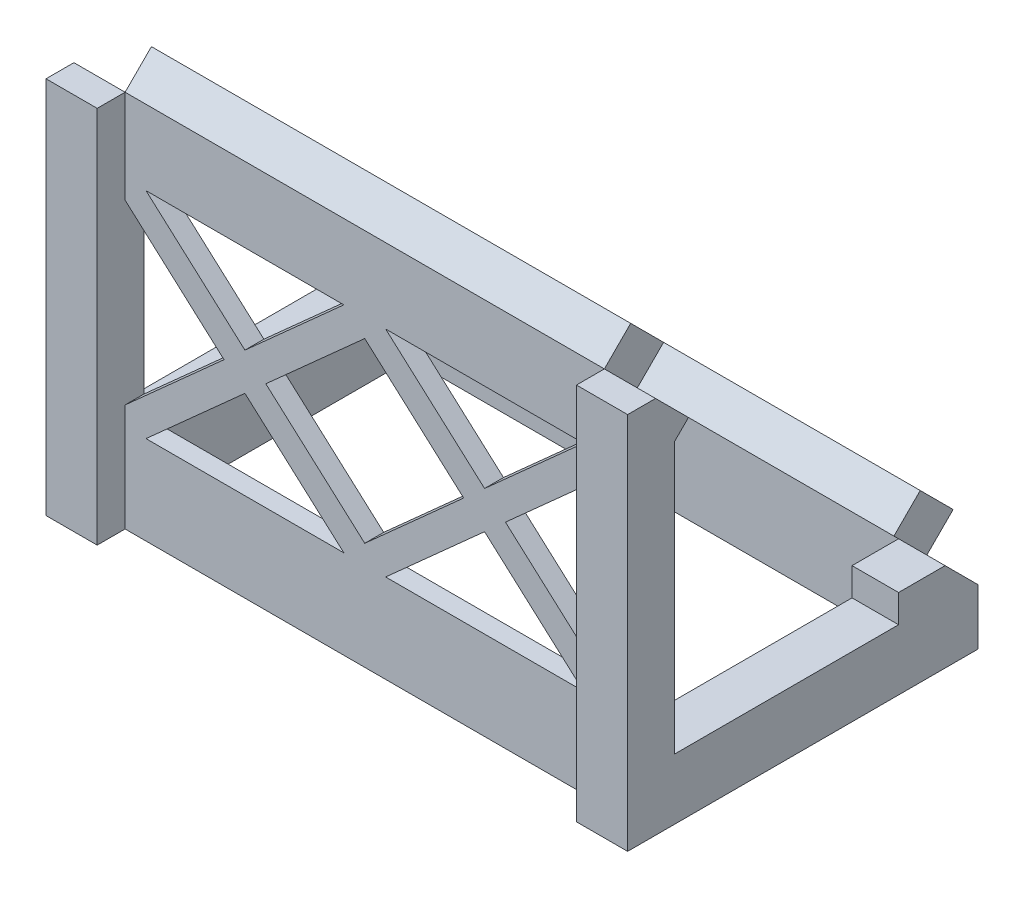
SolidWorks part; units mm, degrees
other "Markup1"
sketch "Sketch33" plane through (0, 74.9533, -74.9533) normal (0.1304, 0.6391, -0.758) x (-0.8301, -0.3477, -0.436)
ref_plane "Front Plane" through (0, 0, 0) normal (0, 0, 1) x (1, 0, 0)
ref_plane "Top Plane" through (0, 0, 0) normal (0, 1, 0) x (1, 0, 0)
ref_plane "Right Plane" through (0, 0, 0) normal (1, 0, 0) x (0, 0, -1)
sketch "Sketch1" plane through (0, 0, 0) normal (1, 0, 0) x (0, 0, -1)
  line L0 (0, 0) -> (69.2965, 0)
  line L1 (69.2965, 0) -> (0, 69.2965)
  line L2 (0, 69.2965) -> (0, 0)
  dimension "D1" = 45
  dimension "D2" = 98
extrude "Boss-Extrude3" add sketch "Sketch1" against normal blind 125
sketch "Sketch3" plane through (0, 0, 0) normal (0, -1, 0) x (1, 0, 0)
  line L1 (0, -69.2965) -> (-125, -69.2965)
  line L2 (0, -69.2965) -> (0, 0)
  line L3 (0, 0) -> (-125, 0)
  line L4 (-125, -69.2965) -> (-125, 0)
  line L5 (0, -69.2965) -> (-125, 0) construction
  line L6 (0, 0) -> (-125, -69.2965) construction
  point P4 (-62.5, -34.6482)
extrude "Boss-Extrude5" add sketch "Sketch3" along normal blind 12
sketch "Sketch6" plane through (-125, 0, 0) normal (-1, 0, 0) x (0, 0, 1)
  line L0 (-69.2965, 0) -> (-62.2254, 7.0711)
  line L1 (-69.2965, 0) -> (0, 69.2965) construction
  line L2 (0, 69.2965) -> (-7.0711, 62.2254)
  line L3 (-62.2254, 7.0711) -> (-7.0711, 7.0711)
  line L4 (-7.0711, 7.0711) -> (-7.0711, 62.2254)
  line L5 (-62.2254, 7.0711) -> (-7.0711, 62.2254)
  line M2 (0, 69.2965) -> (-69.2965, 0)
  dimension "D1" = 10
  dimension "D2" = 10
extrude "Cut-Extrude1" cut sketch "Sketch6" against normal through all contours L3 L4 M2
sketch "Sketch7" plane through (0, 34.6482, -34.6482) normal (0, 0.7071, -0.7071) x (1, 0, 0)
  line L0 (0, 39) -> (-10, 39)
  line L1 (0, 39) -> (-125, 39) construction
  line L2 (-125, 39) -> (-115, 39)
  line L3 (-125, 49) -> (0, 49) construction
  line L4 (-10, 39) -> (-115, 39)
  line L5 (-10, 39) -> (-10, 49)
  line L6 (-10, 49) -> (-115, 49)
  line L7 (-115, 39) -> (-115, 49)
  line L8 (-10, 39) -> (-115, 49) construction
  line L9 (-10, 49) -> (-115, 39) construction
  point P10 (-62.5, 44)
  line M3 (-125, 39) -> (0, 39)
  line M5 (0, 49) -> (-125, 49)
  dimension "D1" = 10
  dimension "D2" = 10
extrude "Boss-Extrude6" add sketch "Sketch7" along normal blind 8 contours L7 L5 M3 M5
sketch "Sketch8" plane through (0, 34.6482, -34.6482) normal (0, 0.7071, -0.7071) x (1, 0, 0)
  line L0 (0, -49) -> (-10, -49)
  line L1 (-125, -49) -> (0, -49) construction
  line L2 (-125, -49) -> (-115, -49)
  line L3 (0, -39) -> (-125, -39) construction
  line L4 (-10, -49) -> (-115, -49)
  line L5 (-10, -49) -> (-10, -39)
  line L6 (-10, -39) -> (-115, -39)
  line L7 (-115, -49) -> (-115, -39)
  line L8 (-10, -49) -> (-115, -39) construction
  line L9 (-10, -39) -> (-115, -49) construction
  point P10 (-62.5, -44)
  line M3 (0, -39) -> (-125, -39)
  line M5 (-125, -49) -> (0, -49)
  dimension "D1" = 10
  dimension "D2" = 10
extrude "Boss-Extrude7" add sketch "Sketch8" along normal blind 8 contours L7 L5 M5 M3
sketch "Sketch9" plane through (0, 7.0711, 0) normal (0, 1, 0) x (1, 0, 0)
  line L0 (0, 62.2254) -> (-10, 62.2254)
  line L1 (-125, 62.2254) -> (-115, 62.2254)
  line L2 (0, 7.0711) -> (-125, 7.0711) construction
  line L3 (-10, 62.2254) -> (-115, 62.2254)
  line L4 (-10, 62.2254) -> (-10, 7.0711)
  line L5 (-10, 7.0711) -> (-115, 7.0711)
  line L6 (-115, 62.2254) -> (-115, 7.0711)
  line L7 (-10, 62.2254) -> (-115, 7.0711) construction
  line L8 (-10, 7.0711) -> (-115, 62.2254) construction
  point P10 (-62.5, 34.6482)
  line M2 (-125, 7.0711) -> (0, 7.0711)
  line M5 (-10, 62.2254) -> (-115, 62.2254)
extrude "Cut-Extrude2" cut sketch "Sketch9" against normal through all contours L6 L4 M5 M2
sketch "Sketch11" plane through (0, 7.0711, 0) normal (0, 1, 0) x (1, 0, 0)
  line L1 (0, 62.2254) -> (-10, 62.2254)
  line L2 (0, 62.2254) -> (0, 7.0711)
  line L3 (0, 7.0711) -> (-10, 7.0711)
  line L4 (-10, 62.2254) -> (-10, 7.0711)
  line L5 (0, 62.2254) -> (-10, 7.0711) construction
  line L6 (0, 7.0711) -> (-10, 62.2254) construction
  point P4 (-5, 34.6482)
extrude "Cut-Extrude3" cut sketch "Sketch11" against normal blind 6
sketch "Sketch12" plane through (0, 7.0711, 0) normal (0, 1, 0) x (1, 0, 0)
  line L1 (-115, 62.2254) -> (-125, 62.2254)
  line L2 (-115, 62.2254) -> (-115, 7.0711)
  line L3 (-115, 7.0711) -> (-125, 7.0711)
  line L4 (-125, 62.2254) -> (-125, 7.0711)
  line L5 (-115, 62.2254) -> (-125, 7.0711) construction
  line L6 (-115, 7.0711) -> (-125, 62.2254) construction
  point P4 (-120, 34.6482)
extrude "Cut-Extrude4" cut sketch "Sketch12" against normal blind 6
sketch "Sketch13" plane through (0, 0, -7.0711) normal (0, 0, -1) x (-1, 0, 0)
  line L1 (10, 1.0711) -> (115, 1.0711)
  line L2 (10, 1.0711) -> (10, 62.2254)
  line L3 (10, 62.2254) -> (115, 62.2254)
  line L4 (115, 1.0711) -> (115, 62.2254)
  line L5 (10, 1.0711) -> (115, 62.2254) construction
  line L6 (10, 62.2254) -> (115, 1.0711) construction
  point P4 (62.5, 31.6482)
extrude "Cut-Extrude6" cut sketch "Sketch13" against normal blind 3
sketch "Sketch14" plane through (0, 34.6482, -34.6482) normal (0, 0.7071, -0.7071) x (1, 0, 0)
  line L0 (0, 49) -> (-6.25, 49)
  line L1 (-10, 49) -> (0, 49) construction
  line L2 (-6.25, 49) -> (-6.25, 42.75)
  circle A0 centre (-6.25, 42.75) radius 1.9
  dimension "D1" = 6.25
  dimension "D2" = 6.25
extrude "Cut-Extrude8" cut sketch "Sketch14" against normal blind 6
ref_plane "Plane1" through (-62.5, 0, 0) normal (1, 0, 0) x (0, 0, -1)
mirror "Mirror1" about plane through (-62.5, 0, 0) normal (1, 0, 0) of "Cut-Extrude8"
sketch "Sketch15" plane through (0, 34.6482, -34.6482) normal (0, 0.7071, -0.7071) x (1, 0, 0)
  line L0 (0, -49) -> (-6.25, -49)
  line L1 (-10, -49) -> (0, -49) construction
  line L2 (-6.25, -49) -> (-6.25, -42.75)
  circle A0 centre (-6.25, -42.75) radius 1.9
  dimension "D3" = 3.8
  dimension "D1" = 6.25
  dimension "D2" = 6.25
extrude "Cut-Extrude9" cut sketch "Sketch15" against normal blind 6
mirror "Mirror2" about plane through (-62.5, 0, 0) normal (1, 0, 0) of "Cut-Extrude9"
sketch "Sketch22" plane through (-10, 0, 0) normal (-1, 0, 0) x (0, 0, 1)
  line L0 (-7.0711, 62.2254) -> (-4.0711, 59.2254)
  line L1 (-4.0711, 62.2254) -> (-4.0711, 1.0711) construction
  line L2 (-4.0711, 59.2254) -> (-4.0711, 62.2254)
  line L3 (-4.0711, 62.2254) -> (-7.0711, 62.2254)
  line L4 (-12.7279, 67.8823) -> (-7.0711, 62.2254) construction
extrude "Boss-Extrude9" add sketch "Sketch22" along normal up to next
sketch "Sketch25" plane through (0, 0, -62.2254) normal (0, 0, 1) x (1, 0, 0)
  line L1 (-10, 1.0711) -> (0, 1.0711)
  line L2 (-10, 1.0711) -> (-10, 7.0711)
  line L3 (-10, 7.0711) -> (0, 7.0711)
  line L4 (0, 1.0711) -> (0, 7.0711)
  line L5 (-10, 1.0711) -> (0, 7.0711) construction
  line L6 (-10, 7.0711) -> (0, 1.0711) construction
  line L7 (-125, 1.0711) -> (-115, 1.0711)
  line L8 (-125, 1.0711) -> (-125, 7.0711)
  line L9 (-125, 7.0711) -> (-115, 7.0711)
  line L10 (-115, 1.0711) -> (-115, 7.0711)
  line L11 (-125, 1.0711) -> (-115, 7.0711) construction
  line L12 (-125, 7.0711) -> (-115, 1.0711) construction
  point P4 (-5, 4.0711)
  point P11 (-120, 4.0711)
extrude "Boss-Extrude13" add sketch "Sketch25" along normal blind 10
sketch "Sketch26" plane through (-10, 0, 0) normal (1, 0, 0) x (0, 0, -1)
  line L0 (0, 69.2965) -> (7.0711, 62.2254)
  line L1 (7.0711, 62.2254) -> (12.7279, 67.8823)
  line L2 (12.7279, 67.8823) -> (5.6569, 74.9533)
  line L3 (5.6569, 74.9533) -> (0, 69.2965)
extrude "Cut-Extrude10" cut sketch "Sketch26" against normal blind 1
sketch "Sketch27" plane through (-10, 0, 0) normal (1, 0, 0) x (0, 0, -1)
  line L0 (62.2254, 7.0711) -> (69.2965, 0)
  line L1 (69.2965, 0) -> (74.9533, 5.6569)
  line L2 (74.9533, 5.6569) -> (67.8823, 12.7279)
  line L3 (67.8823, 12.7279) -> (62.2254, 7.0711)
extrude "Cut-Extrude11" cut sketch "Sketch27" against normal blind 1
mirror "Mirror3" about plane through (-62.5, 0, 0) normal (1, 0, 0) of "Cut-Extrude11", "Cut-Extrude10"
sketch "Sketch29" plane through (0, 0, 0) normal (0, 0, 1) x (1, 0, 0)
  line L0 (-11, 69.2965) -> (0, 69.2965)
  line L1 (0, 69.2965) -> (0, -12)
  line L2 (0, -12) -> (-11, -12)
  line L3 (0, -12) -> (-125, -12) construction
  line L4 (-11, -12) -> (-11, 69.2965)
extrude "Boss-Extrude15" add sketch "Sketch29" along normal blind 6
mirror "Mirror4" about plane through (-62.5, 0, 0) normal (1, 0, 0) of "Boss-Extrude15"
sketch "Sketch31" plane through (0, 34.6482, -34.6482) normal (0, 0.7071, -0.7071) x (1, 0, 0)
  circle A0 centre (-6.25, 42.75) radius 2
  dimension "D1" = 4
extrude "Cut-Extrude16" cut sketch "Sketch31" against normal blind 6
sketch "Sketch32" plane through (0, 34.6482, -34.6482) normal (0, 0.7071, -0.7071) x (1, 0, 0)
  circle A0 centre (-6.25, -42.75) radius 2
  dimension "D1" = 4
extrude "Cut-Extrude17" cut sketch "Sketch32" against normal blind 6
mirror "Mirror5" about plane through (-62.5, 0, 0) normal (1, 0, 0) of "Cut-Extrude17", "Cut-Extrude16"
ref_plane "Plane2" through (-10, 62.2254, -7.0711) normal (1, 0, 0) x (0, 0, -1)
sketch "Sketch41" plane through (-10, 0, 0) normal (-1, 0, 0) x (0, 0, 1)
  line L0 (-7.0711, 1.0711) -> (-4.0711, 1.0711)
  line L1 (-4.0711, 1.0711) -> (-4.0711, 59.2254)
  line L2 (-4.0711, 59.2254) -> (-7.0711, 62.2254)
  line L3 (-7.0711, 62.2254) -> (-4.0711, 59.2254) construction
  line L4 (-7.0711, 62.2254) -> (-7.0711, 1.0711) construction
  line L5 (-7.0711, 62.2254) -> (-7.0711, 1.0711)
extrude "Cut-Extrude22" cut sketch "Sketch41" against normal through all
sketch "Sketch42" plane through (-115, 0, 0) normal (1, 0, 0) x (0, 0, -1)
  line L0 (7.0711, 1.0711) -> (4.0711, 1.0711)
  line L1 (4.0711, 1.0711) -> (4.0711, 59.2254)
  line L2 (4.0711, 59.2254) -> (7.0711, 62.2254)
  line L3 (7.0711, 62.2254) -> (4.0711, 59.2254) construction
  line L4 (7.0711, 1.0711) -> (7.0711, 62.2254) construction
  line L5 (7.0711, 62.2254) -> (7.0711, 1.0711)
extrude "Cut-Extrude23" cut sketch "Sketch42" against normal through all
sketch "Sketch43" plane through (0, 0, -4.0711) normal (0, 0, -1) x (-1, 0, 0)
  line L0 (0, 59.2254) -> (0, 53.2254)
  line L1 (0, 53.2254) -> (11, 53.2254)
  line L2 (0, 1.0711) -> (0, 59.2254) construction
  line L3 (0, 1.0711) -> (0, 7.0711)
  line L4 (0, 7.0711) -> (11, 7.0711)
  line L5 (11, 53.2254) -> (125, 53.2254)
  line L6 (125, 59.2254) -> (125, 1.0711) construction
  line L7 (0, 7.0711) -> (125, 7.0711)
  line L8 (11, 53.2254) -> (62.5, 7.0711)
  line L9 (125, 53.2254) -> (114, 53.2254)
  line L10 (62.5, 7.0711) -> (114, 53.2254)
  line L11 (11, 53.2254) -> (13.1376, 55.3303)
  line L12 (13.1376, 55.3303) -> (66.9863, 7.0711)
  line L13 (11, 53.2254) -> (8.8986, 51.0843)
  line L14 (8.8986, 51.0843) -> (58.0096, 7.0711)
  line L15 (114, 53.2254) -> (116.1254, 51.1082)
  line L16 (116.1254, 51.1082) -> (66.9878, 7.0711)
  line L17 (114, 53.2254) -> (111.911, 55.3785)
  line L18 (111.911, 55.3785) -> (58.0085, 7.0711)
  line L19 (11, 7.0711) -> (62.5, 53.2254)
  line L20 (62.5, 53.2254) -> (114, 7.0711)
  line L21 (11, 7.0711) -> (13.1388, 4.9674)
  line L22 (13.1388, 4.9674) -> (66.9861, 53.2254)
  line L23 (11, 7.0711) -> (8.8787, 9.1924)
  line L24 (8.8787, 9.1924) -> (58.0117, 53.2254)
  line L25 (114, 7.0711) -> (116.1213, 9.1924)
  line L26 (116.1213, 9.1924) -> (66.9883, 53.2254)
  line L27 (114, 7.0711) -> (111.8787, 4.9497)
  line L28 (111.8787, 4.9497) -> (58.0117, 53.2254)
  line L29 (11, 7.0711) -> (11, 53.2254)
  line L30 (114, 7.0711) -> (114, 53.2254)
  dimension "D1" = 6
  dimension "D2" = 11
  dimension "D3" = 6
  dimension "D4" = 11
  dimension "D5" = 11
  dimension "D6" = 3
  dimension "D7" = 3
  dimension "D8" = 3
  dimension "D9" = 3
  dimension "D10" = 3
  dimension "D11" = 3
  dimension "D12" = 3
  dimension "D13" = 3
extrude "Cut-Extrude26" cut sketch "Sketch43" against normal up to next contours L12 L24 L5 | L29 L24 L14 | L22 L7 L18 L14 | L18 L28 L22 L12 | L7 L28 L16 | L26 L30 L16 | L26 L18 L5
